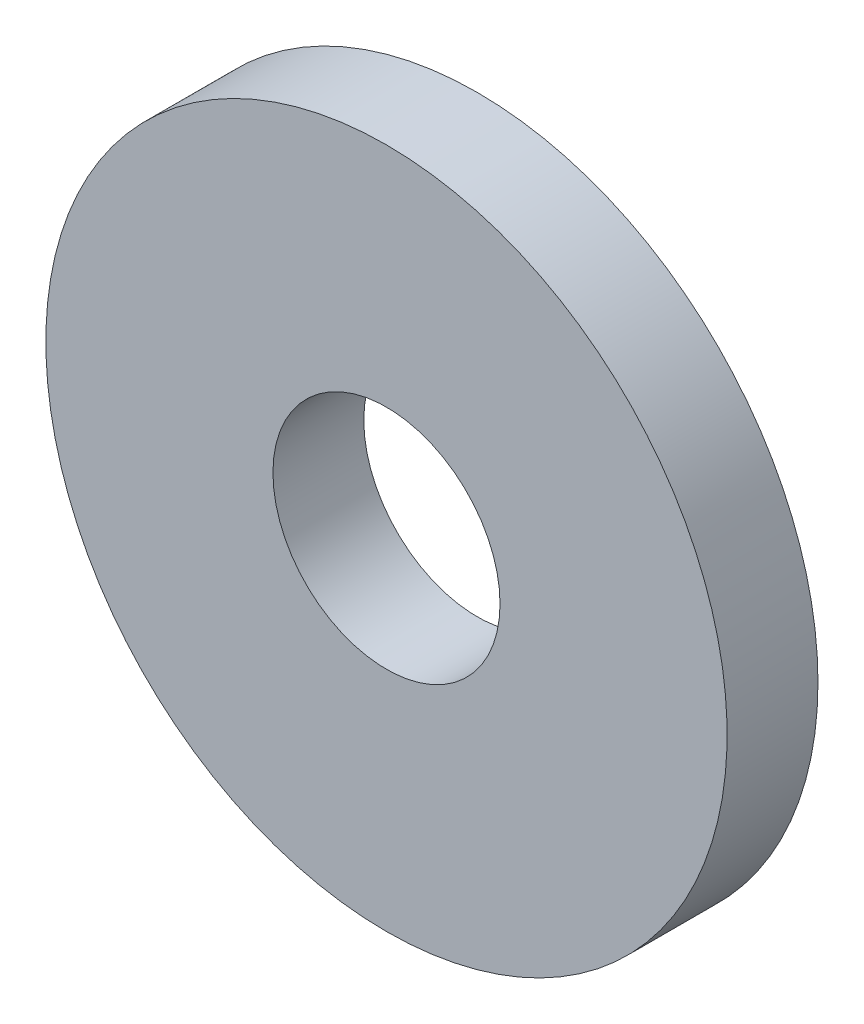
SolidWorks part; units mm, degrees
ref_plane "Front Plane" through (0, 0, 0) normal (0, 0, 1) x (1, 0, 0)
ref_plane "Top Plane" through (0, 0, 0) normal (0, 1, 0) x (1, 0, 0)
ref_plane "Right Plane" through (0, 0, 0) normal (1, 0, 0) x (0, 0, -1)
sketch "Sketch2" plane through (0, 0, 0) normal (0, 0, 1) x (1, 0, 0)
  line L0 (0, 0) -> (0, 60.412) construction
  line L1 (-96.5324, -69.4145) -> (-37.5604, 23.7701)
  line L2 (-104.0638, 80.01) -> (133.9596, 80.01) construction
  line L3 (-104.0638, 80.01) -> (-104.0638, -93.98) construction
  line L4 (-104.0638, -93.98) -> (133.9596, -93.98) construction
  line L5 (133.9596, 80.01) -> (133.9596, -93.98) construction
  line L6 (-81.2499, -86.8063) -> (18.7436, -40.3049)
  line L7 (109.7428, -87.205) -> (-15.1907, -41.7737)
  line L8 (32.7016, 30.1066) -> (122.7421, -67.6946)
  line L9 (-104.0638, -81.28) -> (133.9596, -81.28) construction
  circle A0 centre (0, 0) radius 26 construction
  circle A1 centre (24.7487, 24.7487) radius 3.5
  circle A2 centre (0, 0) radius 35 construction
  circle A3 centre (0, 35) radius 3.5
  circle A4 centre (35, 0) radius 3.5
  circle A5 centre (24.7487, -24.7487) radius 3.5
  circle A6 centre (0, -35) radius 3.5
  circle A7 centre (-24.7487, -24.7487) radius 3.5
  circle A8 centre (-35, 0) radius 3.5
  circle A9 centre (-24.7487, 24.7487) radius 3.5
  circle A10 centre (-86.3375, -75.8664) radius 3.175 construction
  circle A11 centre (113.866, -75.8664) radius 3.175
  circle A12 centre (-104.0638, -93.98) radius 12.7 construction
  circle A13 centre (133.9596, -93.98) radius 12.7 construction
  circle A14 centre (-86.3375, -75.8664) radius 12.065
  circle A15 centre (113.866, -75.8664) radius 12.065
  circle A16 centre (0, 0) radius 44.45
  circle A17 centre (-86.3375, -75.8664) radius 3.175
  circle A18 centre (-86.3375, -75.8664) radius 9.525
  circle A21 centre (0, 0) radius 111.755 construction
  circle A23 centre (0, 0) radius 103.5 construction
  point P23 (0, 0)
  dimension "D1" = 52
  dimension "D2" = 70
  dimension "D3" = 7
  dimension "D9" = 6.35
  dimension "D10" = 25.4
  dimension "D15" = 24.13
  dimension "D16" = 88.9
  dimension "D20" = 207
  dimension "D11" = 19.05
  dimension "D5" = 238.0234
  dimension "D6" = 173.99
  dimension "D7" = 104.0638
  dimension "D8" = 93.98
  dimension "D21" = 8.255
  dimension "D4" = 8
extrude "Boss-Extrude1" add sketch "Sketch2" along normal up to surface (2.54 mm away) contours A18 A17 | A17
ref_plane "Plane1" through (0, 0, 1.27) normal (0, 0, -1) x (-1, 0, 0)
sketch "Sketch3" plane through (0, 0, 2.54) normal (0, 0, 1) x (1, 0, 0)
  circle A1 centre (-86.3375, -75.8664) radius 3.175
  circle A3 centre (-86.3375, -75.8664) radius 9.525 construction
  dimension "D1" = 6.35
extrude "Cut-Extrude1" cut sketch "Sketch3" against normal blind 19.05
